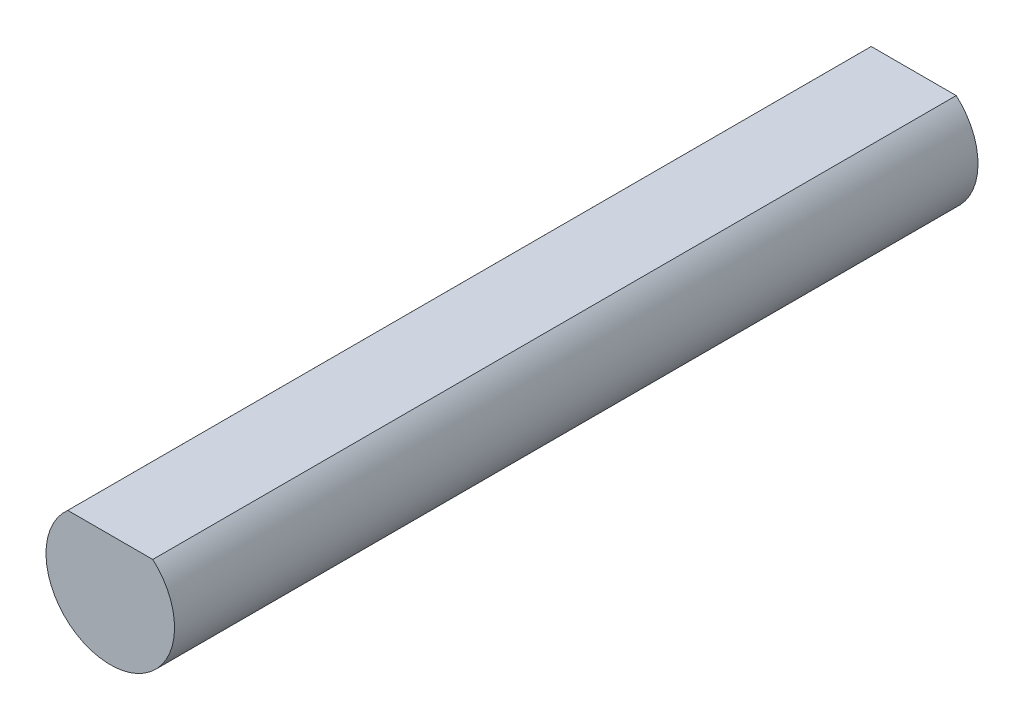
SolidWorks part; units mm, degrees
ref_plane "Front Plane" through (0, 0, 0) normal (0, 0, 1) x (1, 0, 0)
ref_plane "Top Plane" through (0, 0, 0) normal (0, 1, 0) x (1, 0, 0)
ref_plane "Right Plane" through (0, 0, 0) normal (1, 0, 0) x (0, 0, -1)
sketch "Sketch1" plane through (0, 0, 0) normal (0, 0, 1) x (1, 0, 0)
  line L0 (-1.3229, 1.5) -> (1.3229, 1.5)
  arc A0 (-1.3229, 1.5) -> (1.3229, 1.5) centre (0, 0) ccw
  dimension "D1" = 4
  dimension "D2" = 1.5
extrude "Boss-Extrude1" add sketch "Sketch1" along normal blind 25
